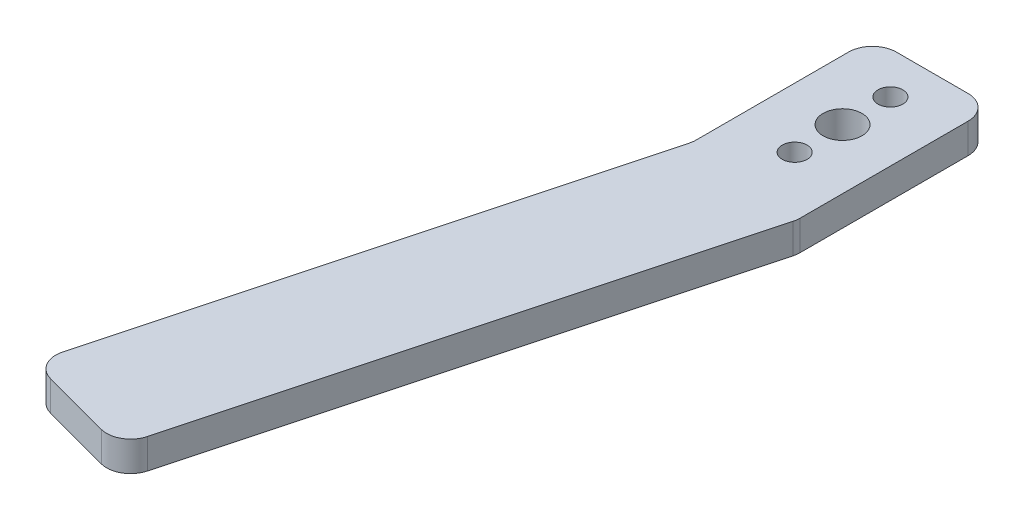
SolidWorks part; units mm, degrees
ref_plane "Front Plane" through (0, 0, 0) normal (0, 0, 1) x (1, 0, 0)
ref_plane "Top Plane" through (0, 0, 0) normal (0, 1, 0) x (1, 0, 0)
ref_plane "Right Plane" through (0, 0, 0) normal (1, 0, 0) x (0, 0, -1)
sketch "Sketch1" plane through (0, 0, 0) normal (0, 1, 0) x (1, 0, 0)
  line L0 (-30, 0) -> (-49.15, 0) construction
  line L1 (-30, -15) -> (30, -15) construction
  line L2 (-30, -15) -> (-30, 15) construction
  line L3 (-30, 15) -> (30, 15) construction
  line L4 (30, -15) -> (30, 15) construction
  line L5 (0, 15) -> (0, -15) construction
  line L6 (-30, 0) -> (30, 0) construction
  line L7 (-59.15, -15) -> (-82.4437, -101.9333)
  line L8 (-59.15, 15) -> (-39.15, 15)
  line L9 (-59.15, 15) -> (-59.15, -15)
  line L10 (-59.15, -15) -> (-39.15, -15) construction
  line L11 (-39.15, 15) -> (-39.15, -15)
  line L12 (-49.15, -15) -> (-49.15, 15) construction
  line L13 (-59.15, 0) -> (-39.15, 0) construction
  line L14 (-59.15, -15) -> (-39.8315, -20.1764) construction
  line L15 (-82.4437, -101.9333) -> (-63.1252, -107.1097)
  line L16 (-39.8315, -20.1764) -> (-63.1252, -107.1097)
  line L17 (-39.8315, -20.1764) -> (-39.15, -17.633)
  line L18 (-39.15, -15) -> (-39.15, -17.633)
  circle A0 centre (-49.15, 0) radius 3.25
  point P0 (0, 0)
  point P14 (-25, 15)
  dimension "D3" = 6.5
  dimension "D1" = 60
  dimension "D2" = 30
  dimension "D4" = 19.15
  dimension "D5" = 20
  dimension "D6" = 30
  dimension "D7" = 20
  dimension "D8" = 90
  dimension "D9" = 165
  dimension "D10" = 5
extrude "Boss-Extrude1" add sketch "Sketch1" along normal blind 5
sketch "Sketch2" plane through (0, 5, 0) normal (0, 1, 0) x (1, 0, 0)
  line L0 (-49.15, 15) -> (-49.15, -15.6557) construction
  line L1 (-39.15, 15) -> (-59.15, 15) construction
  circle A0 centre (-49.15, 8) radius 2.075
  circle A1 centre (-49.15, 0) radius 3.25 construction
  dimension "D1" = 4.15
  dimension "D2" = 8
extrude "Cut-Extrude1" cut sketch "Sketch2" against normal through all both and the other way through all
mirror "Mirror1" about plane through (0, 0, 0) normal (0, 0, 1) of "Cut-Extrude1"
fillet "Fillet1" radius 4 6 edges at (-59.15, 2.5, 15) (-59.15, 2.5, -15) (-39.15, 2.5, -15) (-39.15, 2.5, 17.633) (-82.4437, 2.5, 101.9333) (-63.1252, 2.5, 107.1097)
